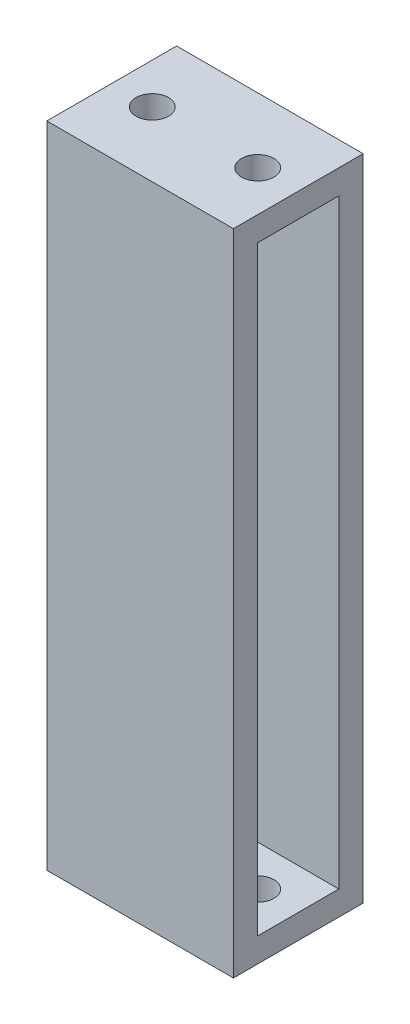
SolidWorks part; units mm, degrees
ref_plane "前视基准面" through (0, 0, 0) normal (0, 0, 1) x (1, 0, 0)
ref_plane "上视基准面" through (0, 0, 0) normal (0, 1, 0) x (1, 0, 0)
ref_plane "右视基准面" through (0, 0, 0) normal (1, 0, 0) x (0, 0, -1)
other "Configuration Table"
sketch "草图1" plane through (0, 0, 0) normal (0, 1, 0) x (1, 0, 0)
  line L0 (-14.1307, 0) -> (13.605, 0) construction
  line L1 (0, 8.9144) -> (0, -9.3719) construction
  line L2 (11.5, 5) -> (11.5, 8)
  line L3 (-1.5, 5) -> (-11.5, 5)
  line L4 (-11.5, 5) -> (-11.5, 8)
  line L5 (1.5, 5) -> (11.5, 5)
  line L6 (-11.5, 8) -> (11.5, 8)
  line L7 (1.5, -5) -> (11.5, -5)
  line L8 (11.5, -5) -> (11.5, -8)
  line L9 (-11.5, -8) -> (11.5, -8)
  line L10 (-11.5, -5) -> (-11.5, -8)
  line L11 (-1.5, -5) -> (-11.5, -5)
  line L12 (-1.5, 5) -> (-1.5, -5)
  line L13 (1.5, 5) -> (1.5, -5)
  dimension "D1" = 1.5
  dimension "D2" = 5
  dimension "D3" = 3
  dimension "D4" = 10
extrude "凸台-拉伸1" add sketch "草图1" along normal blind 80
sketch "草图2" plane through (0, 0, 0) normal (1, 0, 0) x (0, 0, -1)
  line L0 (5, 80) -> (5, 0) construction
  line L1 (-5, 0) -> (5, 0)
  line L2 (-5, 0) -> (-5, 3)
  line L3 (-5, 3) -> (5, 3)
  line L4 (5, 0) -> (5, 3)
  line L5 (5, 80) -> (5, 0) construction
  line L6 (-5, 80) -> (5, 80)
  line L7 (-5, 80) -> (-5, 77)
  line L8 (-5, 77) -> (5, 77)
  line L9 (5, 80) -> (5, 77)
  dimension "D1" = 3
  dimension "D2" = 3
extrude "凸台-拉伸2" add sketch "草图2" along normal mid plane 23
sketch "草图3" plane through (0, 0, 0) normal (0, 1, 0) x (1, 0, 0)
  line L0 (-11.5, 0) -> (11.5, 0) construction
  line L1 (-11.5, 8) -> (-11.5, -8) construction
  line L2 (11.5, -8) -> (11.5, 8) construction
  line L3 (0, 8) -> (0, -8) construction
  line L4 (11.5, 8) -> (-11.5, 8) construction
  line L5 (-11.5, -8) -> (11.5, -8) construction
  circle A0 centre (6.5, 0) radius 2
  circle A1 centre (-6.5, 0) radius 2
  point P14 (0, 0)
  dimension "D1" = 4
  dimension "D2" = 6.5
extrude "切除-拉伸2" cut sketch "草图3" against normal through all and the other way through all
